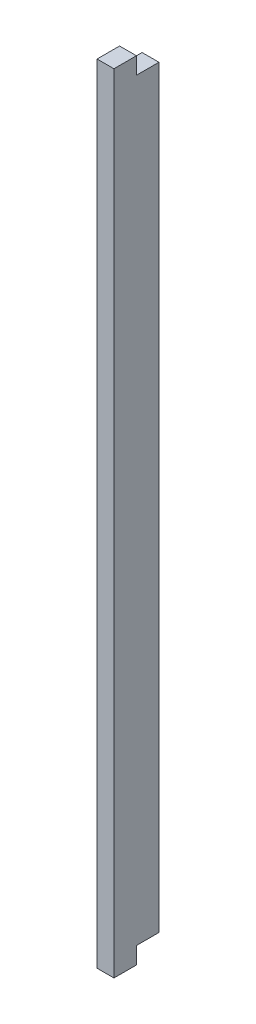
SolidWorks part; units mm, degrees
ref_plane "Front Plane" through (0, 0, 0) normal (0, 0, 1) x (1, 0, 0)
ref_plane "Top Plane" through (0, 0, 0) normal (0, 1, 0) x (1, 0, 0)
ref_plane "Right Plane" through (0, 0, 0) normal (1, 0, 0) x (0, 0, -1)
sketch "Sketch1" plane through (0, 0, 0) normal (1, 0, 0) x (0, 0, -1)
  line L1 (-4, -30.8442) -> (0, -30.8442)
  line L2 (-4, -30.8442) -> (-4, 39.1558)
  line L3 (-4, 39.1558) -> (0, 39.1558)
  line L4 (0, -30.8442) -> (0, 39.1558)
  dimension "D1" = 70
  dimension "D2" = 4
extrude "Boss-Extrude1" add sketch "Sketch1" along normal blind 1.5
sketch "Sketch3" plane through (1.5, 0, 0) normal (1, 0, 0) x (0, 0, -1)
  line L0 (-4, 39.1558) -> (-4, -30.8442) construction
  line L1 (0, 39.1558) -> (-2, 39.1558)
  line L2 (0, 39.1558) -> (0, 37.6558)
  line L3 (0, 37.6558) -> (-2, 37.6558)
  line L4 (-2, 39.1558) -> (-2, 37.6558)
  line L5 (0, -30.8442) -> (-2, -30.8442)
  line L6 (0, -30.8442) -> (0, -29.3442)
  line L7 (0, -29.3442) -> (-2, -29.3442)
  line L8 (-2, -30.8442) -> (-2, -29.3442)
  dimension "D1" = 1.5
  dimension "D2" = 2
extrude "Cut-Extrude1" cut sketch "Sketch3" against normal blind 2
